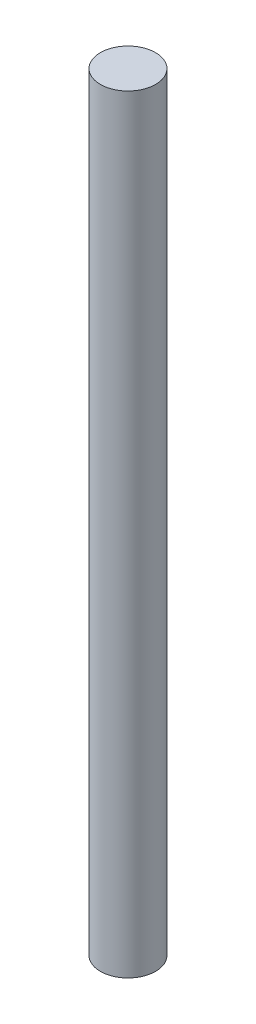
SolidWorks part; units mm, degrees
material "AISI 304"
ref_plane "Front Plane" through (0, 0, 0) normal (0, 0, 1) x (1, 0, 0)
ref_plane "Top Plane" through (0, 0, 0) normal (0, 1, 0) x (1, 0, 0)
ref_plane "Right Plane" through (0, 0, 0) normal (1, 0, 0) x (0, 0, -1)
sketch "Sketch1" plane through (0, 0, 0) normal (0, 1, 0) x (1, 0, 0)
  circle A0 centre (0, 0) radius 4
  dimension "D1" = 8
extrude "Boss-Extrude1" add sketch "Sketch1" along normal mid plane 111.4
